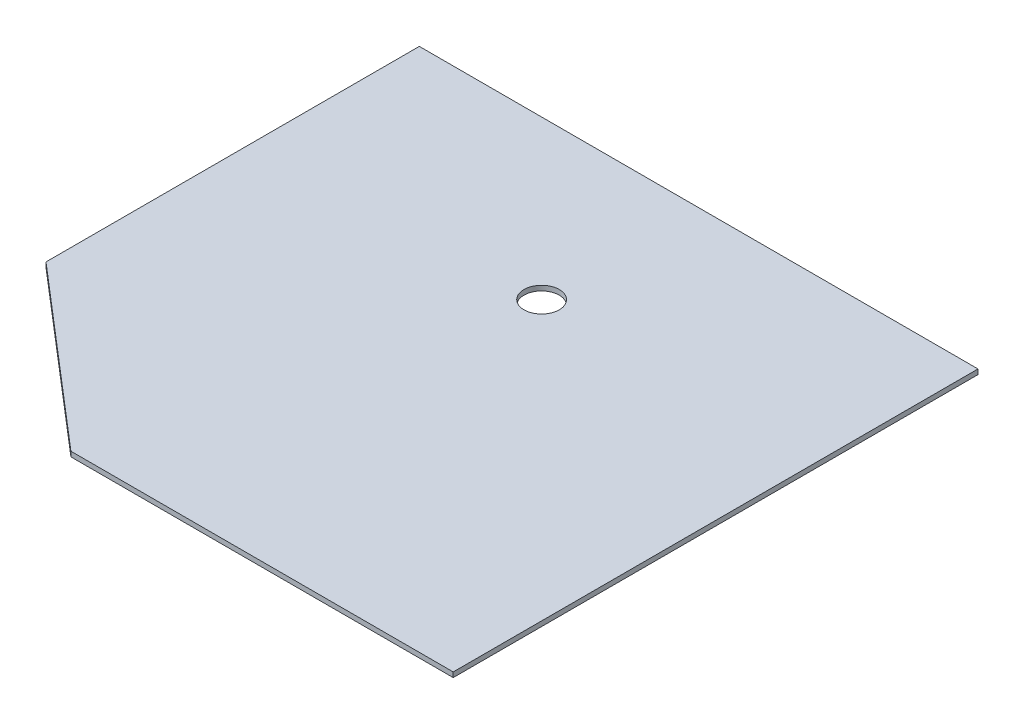
SolidWorks part; units mm, degrees
ref_plane "Front Plane" through (0, 0, 0) normal (0, 0, 1) x (1, 0, 0)
ref_plane "Top Plane" through (0, 0, 0) normal (0, 1, 0) x (1, 0, 0)
ref_plane "Right Plane" through (0, 0, 0) normal (1, 0, 0) x (0, 0, -1)
sketch "Sketch1" plane through (0, 0, 0) normal (0, 1, 0) x (1, 0, 0)
  line L1 (-213.645, -182.0895) -> (238.815, -182.0895)
  line L2 (-213.645, -182.0895) -> (-213.645, 242.9105)
  line L3 (-213.645, 242.9105) -> (238.815, 242.9105)
  line L4 (238.815, -182.0895) -> (238.815, 242.9105)
  dimension "D1" = 452.46
  dimension "D2" = 213.645
  dimension "D3" = 425
extrude "Boss-Extrude1" add sketch "Sketch1" along normal blind 4
sketch "Sketch2" plane through (0, 4, 0) normal (0, -1, 0) x (1, 0, 0)
  line L0 (238.815, -242.9105) -> (-213.645, -242.9105) construction
  line L1 (-213.645, -242.9105) -> (-213.645, 182.0895) construction
  circle A0 centre (13.515, -114.8105) radius 14.275
  dimension "D1" = 28.55
  dimension "D2" = 128.1
  dimension "D3" = 227.16
extrude "Cut-Extrude1" cut sketch "Sketch2" along normal through all
sketch "Sketch3" plane through (0, 4, 0) normal (0, 1, 0) x (1, 0, 0)
  line L0 (-70.7913, -182.0895) -> (-213.645, -59.422)
  line L1 (-213.645, -182.0895) -> (238.815, -182.0895) construction
  line L2 (-213.645, 242.9105) -> (-213.645, -182.0895) construction
  line L3 (-213.645, -59.422) -> (-317.3581, -168.1086)
  line L4 (-317.3581, -168.1086) -> (-142.2182, -320.0924)
  line L5 (-142.2182, -320.0924) -> (-70.7913, -182.0895)
extrude "Cut-Extrude2" cut sketch "Sketch3" against normal through all
sketch "Sketch8" plane through (0, 4, 0) normal (0, 1, 0) x (1, 0, 0)
  line L0 (13.515, 114.8105) -> (13.515, 242.9105)
  line L1 (238.815, 242.9105) -> (-213.645, 242.9105) construction
